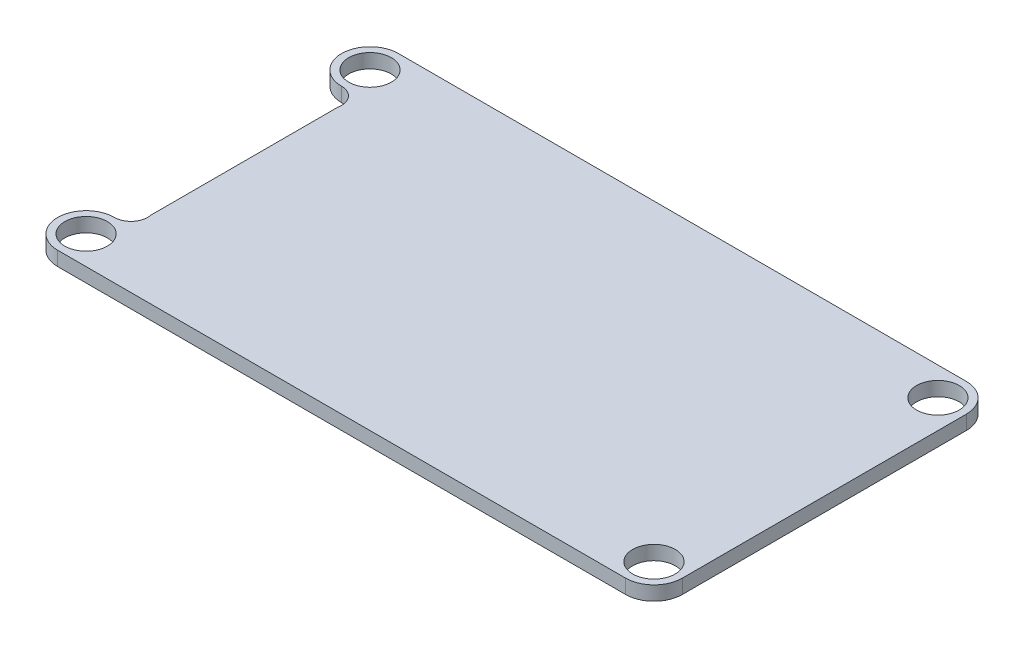
SolidWorks part; units mm, degrees
ref_plane "Front Plane" through (0, 0, 0) normal (0, 0, 1) x (1, 0, 0)
ref_plane "Top Plane" through (0, 0, 0) normal (0, 1, 0) x (1, 0, 0)
ref_plane "Right Plane" through (0, 0, 0) normal (1, 0, 0) x (0, 0, -1)
sketch "Sketch1" plane through (0, 0, 0) normal (0, 1, 0) x (1, 0, 0)
  line L0 (-20, 12) -> (20, 12)
  line L2 (20, -12) -> (-20, -12)
  line L11 (22, 10) -> (22, -10)
  line L13 (-18.86, -6.6) -> (-18.86, 6.6)
  arc A5 (20, 12) -> (22, 10) centre (20, 10) cw
  arc A6 (22, -10) -> (20, -12) centre (20, -10) cw
  arc A8 (-20, 12) -> (-20, 8) centre (-20, 10) ccw
  arc A9 (-20, -12) -> (-20, -8) centre (-20, -10) cw
  arc A10 (-20, 8) -> (-18.86, 6.6) centre (-20, 6.8359) cw
  arc A11 (-20, -8) -> (-18.86, -6.6) centre (-20, -6.8359) ccw
  circle A12 centre (-20, 10) radius 1.5
  circle A13 centre (-20, -10) radius 1.5
  circle A14 centre (20, -10) radius 1.5
  circle A15 centre (20, 10) radius 1.5
extrude "Boss-Extrude1" add sketch "Sketch1" along normal blind 1
